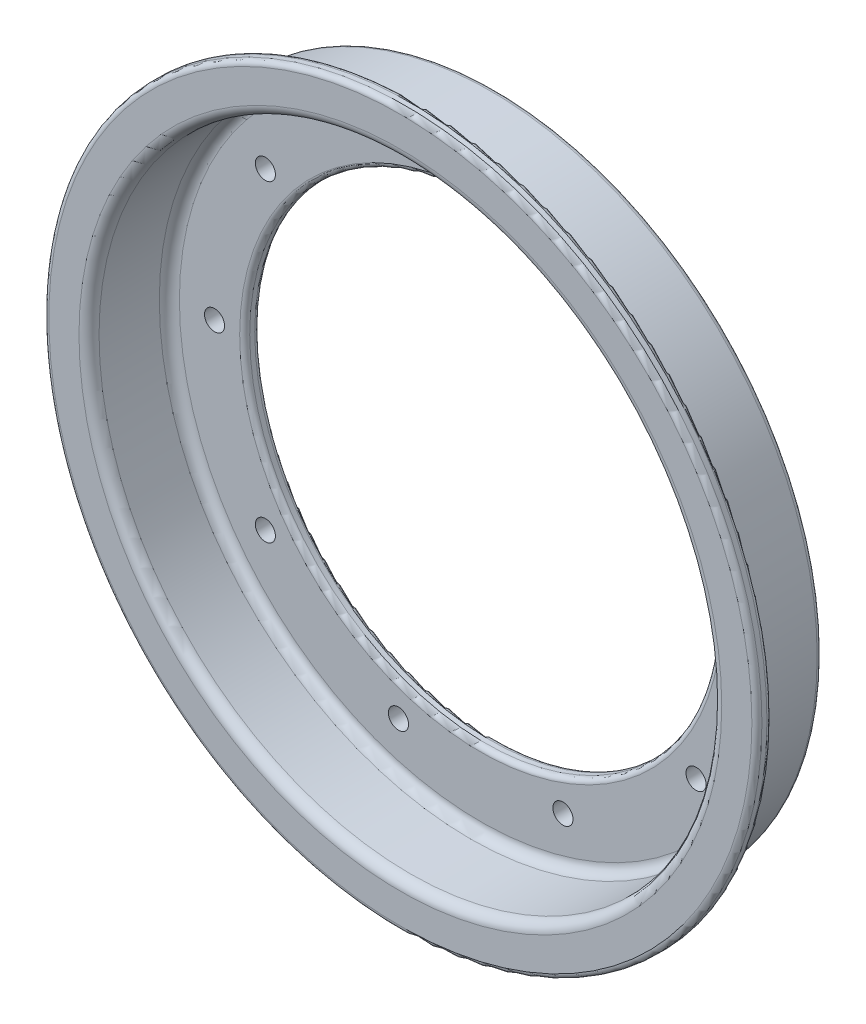
SolidWorks part; units mm, degrees
material "6061 合金"
ref_plane "前视基准面" through (0, 0, 0) normal (0, 0, 1) x (1, 0, 0)
ref_plane "上视基准面" through (0, 0, 0) normal (0, 1, 0) x (1, 0, 0)
ref_plane "右视基准面" through (0, 0, 0) normal (1, 0, 0) x (0, 0, -1)
sketch "草图2" plane through (0, 0, 0) normal (0, 0, 1) x (1, 0, 0)
  circle A0 centre (0, 0) radius 65 construction
  circle A1 centre (0, 0) radius 65 construction
  circle A2 centre (0, 0) radius 71
  circle A4 centre (0, 0) radius 62
  dimension "D1" = 6
  dimension "D3" = 3
extrude "凸台-拉伸1" add sketch "草图2" along normal blind 3
sketch "草图3" plane through (0, 0, 0) normal (0, 0, -1) x (-1, 0, 0)
  circle A0 centre (0, 0) radius 65 construction
  circle A1 centre (0, 0) radius 62 construction
  circle A2 centre (0, 0) radius 65
  circle A3 centre (0, 0) radius 62
  circle M3 centre (0, 0) radius 62
extrude "凸台-拉伸2" add sketch "草图3" along normal offset from surface (16 mm away) 3 contours A2 M3
sketch "草图4" plane through (0, 0, -13) normal (0, 0, -1) x (-1, 0, 0)
  circle A0 centre (0, 0) radius 53 construction
  circle A1 centre (0, 0) radius 47
  circle A2 centre (0, 0) radius 65 construction
  circle A3 centre (0, 0) radius 65
  dimension "D1" = 6
extrude "凸台-拉伸3" add sketch "草图4" along normal blind 3
fillet "圆角1" radius 2 1 edges at (-62, 0, -13)
fillet "圆角2" radius 1 2 edges at (-47, 0, -13) (-47, 0, -16)
fillet "圆角3" radius 2 1 edges at (62, 0, 3)
fillet "圆角4" radius 1 2 edges at (71, 0, 0) (71, 0, 3)
fillet "圆角5" radius 1 1 edges at (-65, 0, -16)
sketch "草图5" plane through (0, 0, 3) normal (0, 0, 1) x (1, 0, 0)
  circle A0 centre (42.8779, 31.1526) radius 2
  circle A1 centre (53, 0) radius 2
  circle A2 centre (42.8779, -31.1526) radius 2
  circle A3 centre (16.3779, -50.406) radius 2
  circle A4 centre (-16.3779, -50.406) radius 2
  circle A5 centre (-42.8779, -31.1526) radius 2
  circle A6 centre (-53, 0) radius 2
  circle A7 centre (-42.8779, 31.1526) radius 2
  circle A8 centre (-16.3779, 50.406) radius 2
  circle A9 centre (16.3779, 50.406) radius 2
  point P24 (0, 0)
  dimension "D1" = 10
extrude "切除-拉伸1" cut sketch "草图5" against normal through all both and the other way through all
